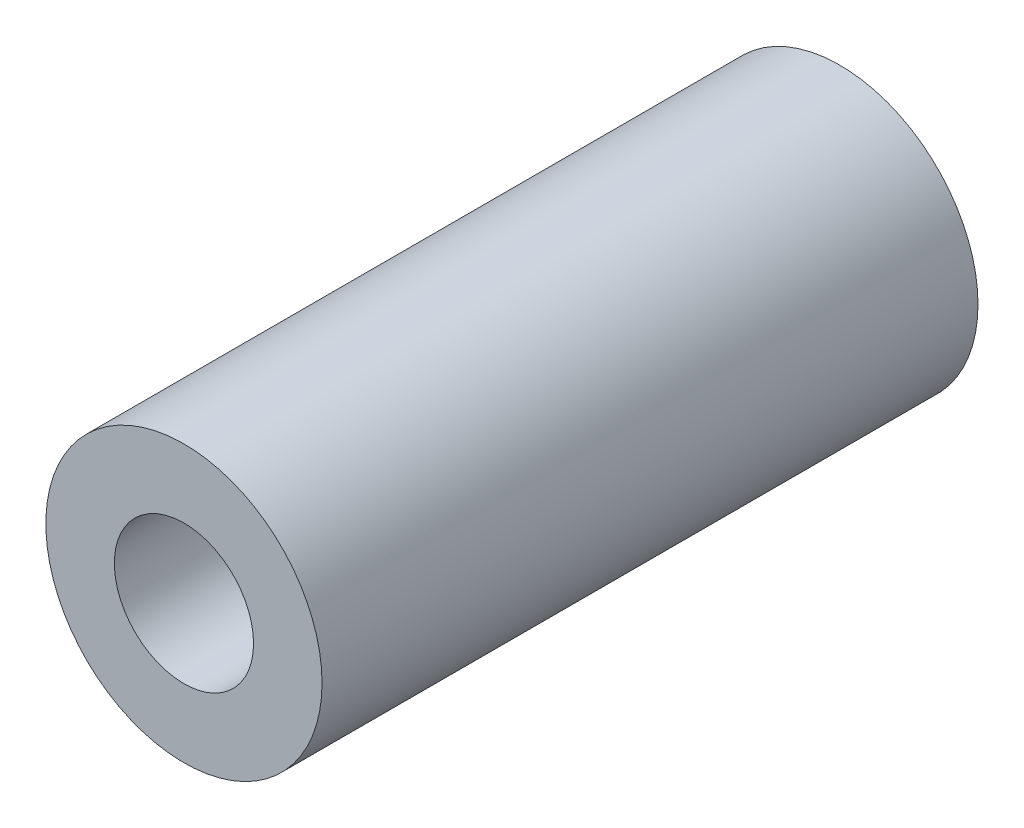
SolidWorks part; units mm, degrees
ref_plane "Front Plane" through (0, 0, 0) normal (0, 0, 1) x (1, 0, 0)
ref_plane "Top Plane" through (0, 0, 0) normal (0, 1, 0) x (1, 0, 0)
ref_plane "Right Plane" through (0, 0, 0) normal (1, 0, 0) x (0, 0, -1)
sketch "Sketch1" plane through (0, 0, 0) normal (0, 0, 1) x (1, 0, 0)
  circle A0 centre (0, 0) radius 6.35
  circle A1 centre (0, 0) radius 3.2004
  dimension "OD" = 12.7
  dimension "ID" = 6.4008
extrude "Extrude1" add sketch "Sketch1" along normal mid plane 30.1625
sketch "Sketch2" plane through (0, 0, 0) normal (1, 0, 0) x (0, 0, -1)
  line L0 (-15.0812, -3.2004) -> (15.0812, -3.2004) construction
  line L3 (15.0812, 3.2004) -> (-15.0812, 3.2004) construction
  line L5 (-15.0812, -3.2004) -> (15.0812, -3.2004)
  line L6 (15.0812, 3.2004) -> (-15.0812, 3.2004)
sketch "Sketch4" plane through (0, 0, 15.0812) normal (0, 0, 1) x (1, 0, 0)
  line L0 (0, 0) -> (-2.263, 2.263)
  line L1 (0, -5.2388) -> (0, 5.2388) construction
  circle A0 centre (0, 0) radius 3.2004 construction
  dimension "D1" = 45
